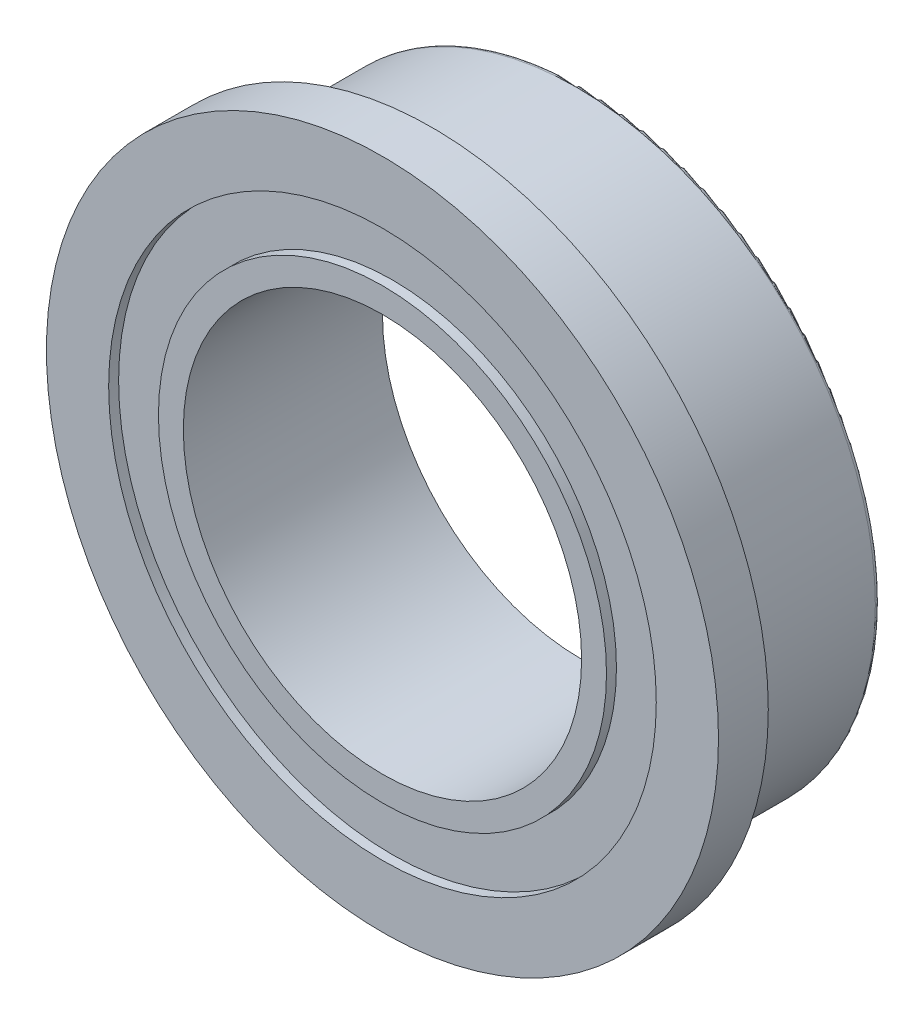
SolidWorks part; units mm, degrees
ref_plane "前基準面" through (0, 0, 0) normal (0, 0, 1) x (1, 0, 0)
ref_plane "上基準面" through (0, 0, 0) normal (0, 1, 0) x (1, 0, 0)
ref_plane "右基準面" through (0, 0, 0) normal (1, 0, 0) x (0, 0, -1)
sketch "草圖1" plane through (0, 0, 0) normal (0, 0, 1) x (1, 0, 0)
  circle A0 centre (0, 0) radius 6
  dimension "D1" = 12
extrude "填料-伸長1" add sketch "草圖1" along normal blind 4
sketch "草圖2" plane through (0, 0, 4) normal (0, 0, 1) x (1, 0, 0)
  circle A0 centre (0, 0) radius 6.75
  dimension "D1" = 13.5
extrude "填料-伸長2" add sketch "草圖2" against normal blind 1
sketch "草圖3" plane through (0, 0, 0) normal (0, 0, -1) x (-1, 0, 0)
  circle A0 centre (0, 0) radius 4
  dimension "D1" = 8
extrude "除料-伸長1" cut sketch "草圖3" against normal through all
sketch "草圖4" plane through (0, 0, 0) normal (0, 0, -1) x (-1, 0, 0)
  circle A0 centre (0, 0) radius 5.5
  circle A1 centre (0, 0) radius 4.5
  circle A2 centre (0, 0) radius 6 construction
  circle A3 centre (0, 0) radius 4 construction
  dimension "D1" = 0.5
  dimension "D2" = 0.5
extrude "除料-伸長2" cut sketch "草圖4" against normal blind 0.2
sketch "草圖5" plane through (0, 0, 4) normal (0, 0, 1) x (1, 0, 0)
  circle A0 centre (0, 0) radius 4.5
  circle A1 centre (0, 0) radius 5.5
  circle A2 centre (0, 0) radius 4 construction
  dimension "D1" = 0.5
  dimension "D2" = 1
extrude "除料-伸長3" cut sketch "草圖5" against normal blind 0.2
fillet "圓角1" radius 0.1 1 edges at (6, 0, 0)
